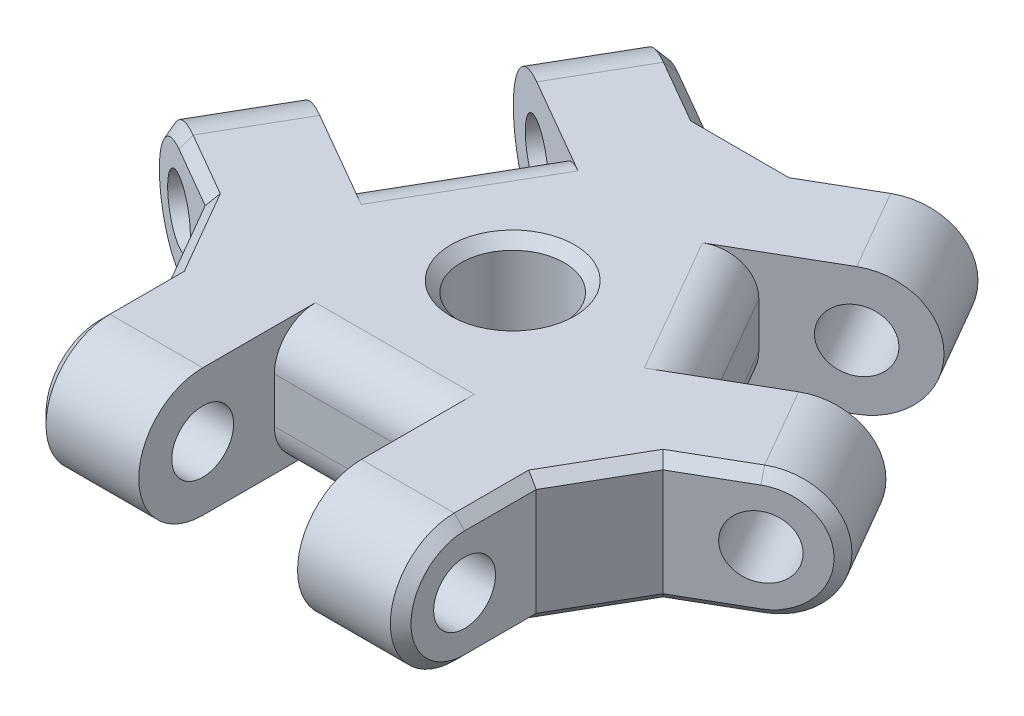
SolidWorks part; units mm, degrees
ref_plane "Front Plane" through (0, 0, 0) normal (0, 0, 1) x (1, 0, 0)
ref_plane "Top Plane" through (0, 0, 0) normal (0, 1, 0) x (1, 0, 0)
ref_plane "Right Plane" through (0, 0, 0) normal (1, 0, 0) x (0, 0, -1)
sketch "Sketch1" plane through (0, 0, 0) normal (0, 1, 0) x (1, 0, 0)
  line L0 (-8.85, -7.7076) -> (-8.85, -14.6576)
  line L1 (-13.35, -7.7076) -> (13.35, -7.7076) construction
  line L6 (-13.35, -7.7076) -> (0, 15.4153) construction
  line L7 (-8.85, -14.6576) -> (-3.85, -14.6576)
  line L8 (-3.85, -14.6576) -> (-3.85, -7.7076)
  line L13 (-8.85, -7.7076) -> (-13.35, -7.7076) construction
  line L39 (0, 15.4153) -> (13.35, -7.7076) construction
  line L40 (-6.675, 3.8538) -> (0, 0) construction
  line L41 (6.675, 3.8538) -> (0, 0) construction
  line L42 (0, 0) -> (0, 15.4153) construction
  line L43 (0, -7.7076) -> (0, 0) construction
  line L44 (-3.85, -7.7076) -> (0, -7.7076) construction
  line L45 (8.85, -7.7076) -> (8.85, -14.6576)
  line L46 (3.85, -14.6576) -> (3.85, -7.7076)
  line L47 (8.85, -14.6576) -> (3.85, -14.6576)
  line L48 (-3.85, -7.7076) -> (3.85, -7.7076)
  line L49 (-2.25, 11.5181) -> (-8.2689, 14.9931)
  line L50 (-8.2689, 14.9931) -> (-10.7689, 10.663)
  line L51 (-10.7689, 10.663) -> (-4.75, 7.188)
  line L52 (-14.6189, 3.9946) -> (-8.6, 0.5196)
  line L53 (-17.1189, -0.3355) -> (-14.6189, 3.9946)
  line L54 (-11.1, -3.8105) -> (-17.1189, -0.3355)
  line L55 (-4.75, 7.188) -> (-8.6, 0.5196)
  line L56 (11.1, -3.8105) -> (17.1189, -0.3355)
  line L57 (17.1189, -0.3355) -> (14.6189, 3.9946)
  line L58 (14.6189, 3.9946) -> (8.6, 0.5196)
  line L59 (10.7689, 10.663) -> (4.75, 7.188)
  line L60 (8.2689, 14.9931) -> (10.7689, 10.663)
  line L61 (2.25, 11.5181) -> (8.2689, 14.9931)
  line L62 (8.6, 0.5196) -> (4.75, 7.188)
  line L63 (-8.85, -7.7076) -> (-11.1, -3.8105)
  line L64 (-2.25, 11.5181) -> (2.25, 11.5181)
  line L65 (8.85, -7.7076) -> (11.1, -3.8105)
  circle A0 centre (0, 0) radius 2.5
  point P0 (0, 0)
  point P17 (0, 0)
  point P18 (0, 0)
  point P26 (0, 0)
  point P30 (0, 0)
  point P35 (0, 0)
  point P41 (0, 0)
  dimension "D1" = 7.7
  dimension "D2" = 5
  dimension "D3" = 3
  dimension "D6" = 6.95
  dimension "D7" = 4.5
extrude "Boss-Extrude1" add sketch "Sketch1" along normal mid plane 6.2
sketch "Sketch2" plane through (-8.85, 0, 0) normal (-1, 0, 0) x (0, 0, 1)
  line L0 (7.7076, 3.1) -> (14.6576, -3.1) construction
  line L1 (7.7076, -3.1) -> (14.6576, 3.1) construction
  line L2 (7.7076, 3.1) -> (14.6576, 3.1) construction
  line L3 (14.6576, 3.1) -> (14.6576, -3.1) construction
  line L4 (11.1826, 3.1) -> (14.6576, 3.1)
  line L5 (14.6576, 3.1) -> (14.6576, -3.1)
  line L6 (14.6576, -3.1) -> (11.1826, -3.1)
  line L7 (7.7076, -3.1) -> (14.6576, -3.1) construction
  circle A0 centre (11.1826, 0) radius 1.5
  arc A1 (11.1826, 3.1) -> (11.1826, -3.1) centre (11.1826, 0) cw
  point P10 (11.1826, 0)
  dimension "D1" = 3
extrude "Cut-Extrude1" cut sketch "Sketch2" against normal through all both and the other way through all
pattern_circular "CirPattern5" count 3 every 120 about axis through (0, 3.1, 0) along (0, -1, 0) of "Cut-Extrude1"
fillet "Fillet2" radius 2 6 edges at (6.675, 3.1, -3.8538) (6.675, -3.1, -3.8538) (-6.675, -3.1, -3.8538) (-6.675, 3.1, -3.8538) (0, 3.1, 7.7076) (0, -3.1, 7.7076)
chamfer "Chamfer1" distance 0.5 angle 45 26 edges at (12.6047, -3.1, 2.9418) (9.975, -3.1, 5.7591) (8.85, -3.1, 9.4451) (16.7941, 0, 0.523) (8.85, 0, 14.2826) (12.6047, 3.1, 2.9418) (9.975, 3.1, 5.7591) (8.85, 3.1, 9.4451) (-12.6047, -3.1, 2.9418) (-9.975, -3.1, 5.7591) (-8.85, -3.1, 9.4451) (-8.85, 0, 14.2826) (-16.7941, 0, 0.523) (-8.85, 3.1, 9.4451) (-9.975, 3.1, 5.7591) (-12.6047, 3.1, 2.9418) (-3.7547, -3.1, -12.3869) (3.7547, -3.1, -12.3869) (0, -3.1, -11.5181) (-7.9441, 0, -14.8056) (7.9441, 0, -14.8056) (-3.7547, 3.1, -12.3869) (3.7547, 3.1, -12.3869) (0, 3.1, -11.5181) (0, -3.1, 2.5) (0, 3.1, 2.5)
